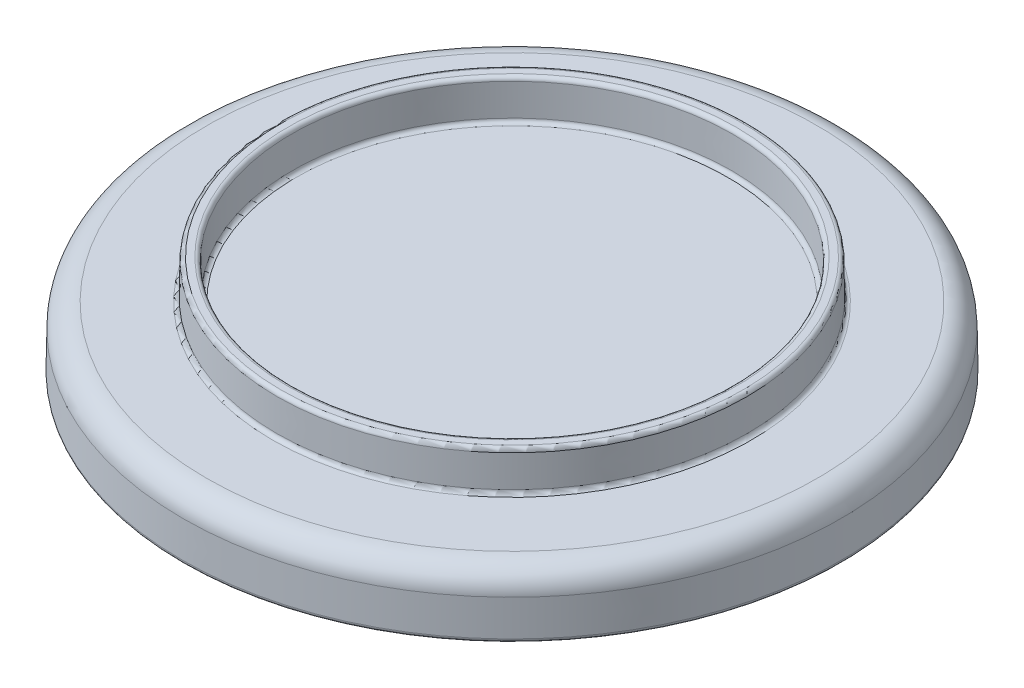
SolidWorks part; units mm, degrees
ref_plane "Front" through (0, 0, 0) normal (0, 0, 1) x (1, 0, 0)
ref_plane "Top" through (0, 0, 0) normal (0, 1, 0) x (1, 0, 0)
ref_plane "Right" through (0, 0, 0) normal (1, 0, 0) x (0, 0, -1)
sketch "Sketch1" plane through (0, 0, 0) normal (0, 1, 0) x (1, 0, 0)
  circle A0 centre (0, 0) radius 40
  dimension "D1" = 80
extrude "Boss-Extrude1" add sketch "Sketch1" along normal blind 6 draft 1 separate body
shell "Shell1" thickness 2
sketch "Sketch2" plane through (0, 8, 0) normal (0, 1, 0) x (1, 0, 0)
  circle A0 centre (0, 0) radius 30
  circle A1 centre (0, 0) radius 28
  dimension "D1" = 60
  dimension "D2" = 2
extrude "Boss-Extrude2" add sketch "Sketch2" along normal blind 5 draft 1
fillet "Fillet1" radius 0.5 4 edges at (0, 0, 40) (0, 0, 42.0003) (0, 13, 28.0873) (0, 13, 29.9127)
fillet "Fillet2" radius 1 1 edges at (0, 6, 39.8953)
fillet "Fillet3" radius 3 1 edges at (0, 8, 41.8607)
fillet "Fillet4" radius 0.5 2 edges at (0, 8, 28) (0, 8, 30)
